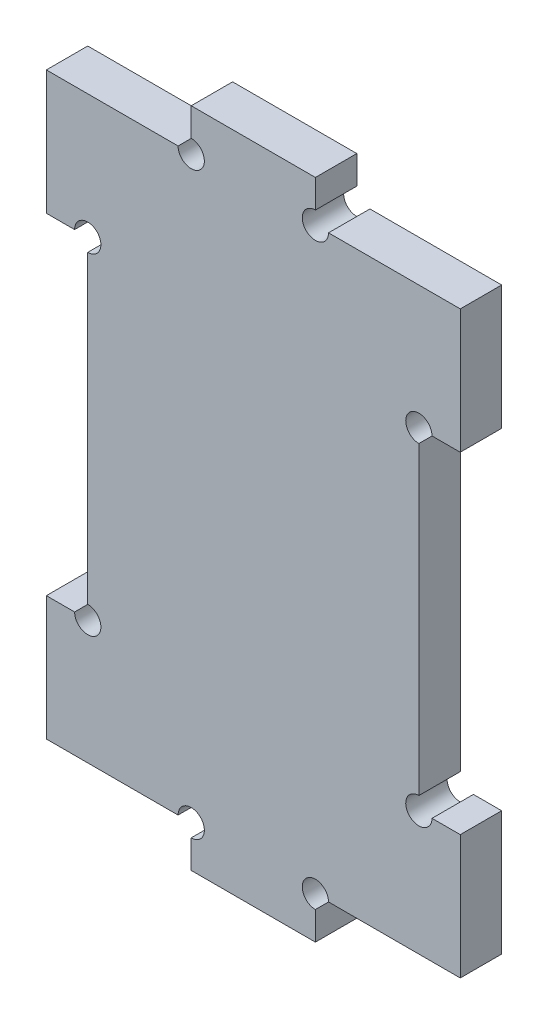
SolidWorks part; units mm, degrees
material "Acrylic (Medium-high impact)"
ref_plane "Front Plane" through (0, 0, 0) normal (0, 0, 1) x (1, 0, 0)
ref_plane "Top Plane" through (0, 0, 0) normal (0, 1, 0) x (1, 0, 0)
ref_plane "Right Plane" through (0, 0, 0) normal (1, 0, 0) x (0, 0, -1)
sketch "Sketch2" plane through (0, 0, 0) normal (0, 0, 1) x (1, 0, 0)
  line L0 (-7.5, 40) -> (7.5, 40)
  line L1 (7.5, 40) -> (7.5, 35)
  line L2 (7.5, 35) -> (25, 35)
  line L3 (25, 35) -> (25, -35)
  line L4 (0, 0) -> (25, 0) construction
  line L5 (0, -40) -> (0, 40) construction
  line L6 (-25, 35) -> (-25, -35)
  line L7 (-7.5, 35) -> (-25, 35)
  line L8 (-7.5, 40) -> (-7.5, 35)
  line L9 (-7.5, -40) -> (-7.5, -35)
  line L10 (-7.5, -35) -> (-25, -35)
  line L11 (7.5, -35) -> (25, -35)
  line L12 (7.5, -40) -> (7.5, -35)
  line L13 (-7.5, -40) -> (7.5, -40)
  point P17 (-25, 0)
  dimension "D1" = 5
  dimension "D2" = 25
  dimension "D3" = 7.5
  dimension "D4" = 40
extrude "Boss-Extrude2" add sketch "Sketch2" along normal blind 5
sketch "Sketch3" plane through (0, 0, 5) normal (0, 0, 1) x (1, 0, 0)
  line L0 (0, 0) -> (-25, 0) construction
  line L1 (-25, 35) -> (-25, -35) construction
  line L3 (-20, -20) -> (-25, -20)
  line L4 (-20, -20) -> (-20, 20)
  line L5 (-20, 20) -> (-25, 20)
  line L6 (-25, -20) -> (-25, 20)
  line L7 (-20, -20) -> (-25, 20) construction
  line L8 (-20, 20) -> (-25, -20) construction
  point P5 (-22.5, 0)
  point P8 (-25, 0)
  dimension "D1" = 40
  dimension "D2" = 5
extrude "Cut-Extrude1" cut sketch "Sketch3" against normal blind 5
mirror "Mirror1" about plane through (0, 0, 0) normal (1, 0, 0) of "Cut-Extrude1"
sketch "Sketch4" plane through (0, 0, 5) normal (0, 0, 1) x (1, 0, 0)
  circle A0 centre (-7.5, 35) radius 1.5875
  circle A1 centre (7.5, 35) radius 1.5875
  circle A2 centre (20, 20) radius 1.5875
  circle A3 centre (-20, 20) radius 1.5875
  circle A4 centre (-20, -20) radius 1.5875
  circle A5 centre (-7.5, -35) radius 1.5875
  circle A6 centre (7.5, -35) radius 1.5875
  circle A7 centre (20, -20) radius 1.5875
  dimension "D1" = 3.175
extrude "Cut-Extrude2" cut sketch "Sketch4" against normal through all
